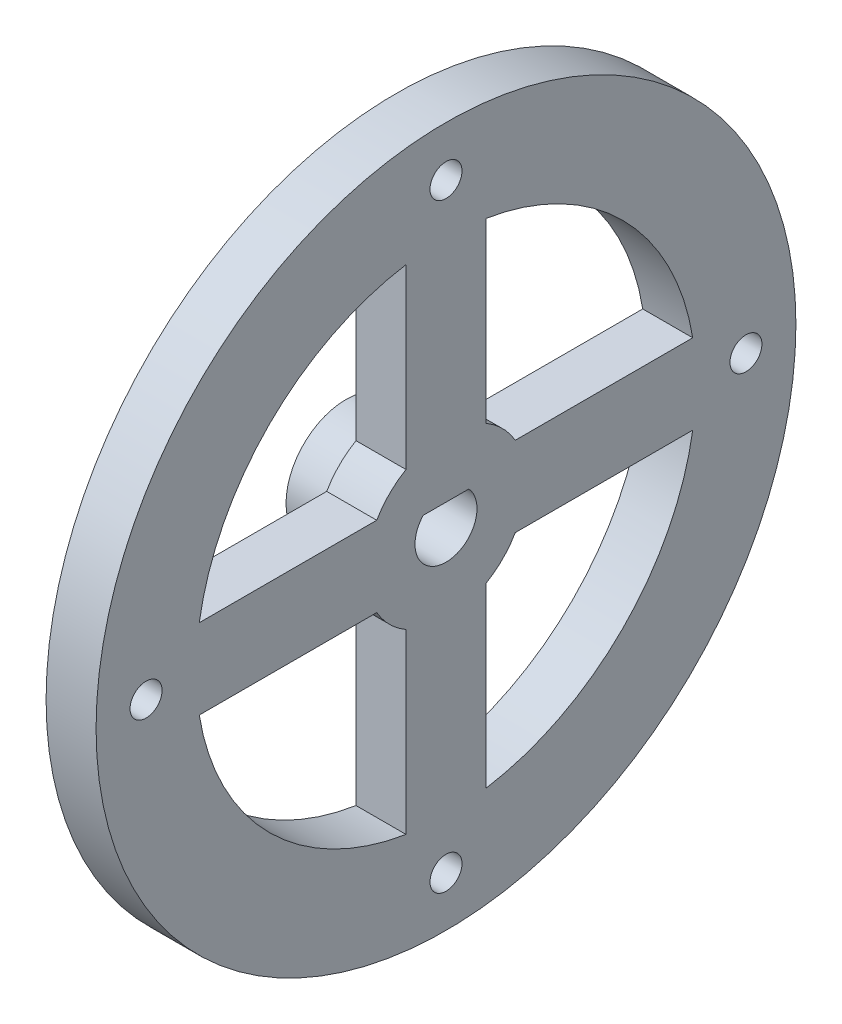
SolidWorks part; units mm, degrees
material "PLA (White)"
ref_plane "Front Plane" through (0, 0, 0) normal (0, 0, 1) x (1, 0, 0)
ref_plane "Top Plane" through (0, 0, 0) normal (0, 1, 0) x (1, 0, 0)
ref_plane "Right Plane" through (0, 0, 0) normal (1, 0, 0) x (0, 0, -1)
sketch "Sketch1" plane through (0, 0, 0) normal (1, 0, 0) x (0, 0, -1)
  line L0 (0, 0) -> (0, 50000) construction
  line L1 (4, 6.9282) -> (4, 24.6779)
  line L2 (-4, 24.6779) -> (-4, 6.9282)
  line L3 (-24.6779, -4) -> (-6.9282, -4)
  line L4 (-6.9282, 4) -> (-24.6779, 4)
  line L5 (4, -24.6779) -> (4, -6.9282)
  line L6 (-4, -6.9282) -> (-4, -24.6779)
  line L7 (24.6779, 4) -> (6.9282, 4)
  line L8 (6.9282, -4) -> (24.6779, -4)
  line L9 (2.2804, 2.1) -> (-2.2804, 2.1)
  circle A0 centre (0, 0) radius 35
  arc A1 (-2.2804, 2.1) -> (2.2804, 2.1) centre (0, 0) ccw
  arc A2 (-6.9282, -4) -> (-4, -6.9282) centre (0, 0) ccw
  arc A3 (-24.6779, -4) -> (-4, -24.6779) centre (0, 0) ccw
  arc A4 (-4, 6.9282) -> (-6.9282, 4) centre (0, 0) ccw
  arc A5 (24.6779, 4) -> (4, 24.6779) centre (0, 0) ccw
  arc A6 (4, -24.6779) -> (24.6779, -4) centre (0, 0) ccw
  arc A7 (4, -6.9282) -> (6.9282, -4) centre (0, 0) ccw
  arc A8 (6.9282, 4) -> (4, 6.9282) centre (0, 0) ccw
  arc A9 (-24.6779, 4) -> (-4, 24.6779) centre (0, 0) cw
  point P27 (0, 0)
  dimension "D1" = 70
  dimension "D2" = 6.2
  dimension "D5" = 16
  dimension "D6" = 50
  dimension "D3" = 8
  dimension "D7" = 2.1
  dimension "D4" = 4
extrude "Boss-Extrude1" add sketch "Sketch1" along normal blind 5
sketch "Sketch2" plane through (0, 0, 0) normal (-1, 0, 0) x (0, 0, 1)
  circle A0 centre (0, 0) radius 30 construction
  circle A1 centre (0, 30) radius 1.6
  circle A2 centre (30, 0) radius 1.6
  circle A3 centre (0, -30) radius 1.6
  circle A4 centre (-30, 0) radius 1.6
  point P14 (0, 0)
  dimension "D1" = 60
  dimension "D2" = 3.2
  dimension "D3" = 4
extrude "Cut-Extrude1" cut sketch "Sketch2" against normal through all
sketch "Sketch3" plane through (0, 0, 0) normal (-1, 0, 0) x (0, 0, 1)
  line L0 (-2.2804, 2.1) -> (2.2804, 2.1) construction
  line L1 (-2.2804, 2.1) -> (2.2804, 2.1)
  circle A2 centre (0, 0) radius 6
  arc A3 (-2.2804, 2.1) -> (2.2804, 2.1) centre (0, 0) ccw construction
  arc A4 (-2.2804, 2.1) -> (2.2804, 2.1) centre (0, 0) ccw
  dimension "D1" = 12
extrude "Boss-Extrude2" add sketch "Sketch3" along normal blind 5
sketch "Sketch6" plane through (0, 0, 0) normal (-1, 0, 0) x (0, 0, 1)
  circle A0 centre (0, 30) radius 4
  circle A1 centre (30, 0) radius 4
  circle A2 centre (0, -30) radius 4
  circle A3 centre (-30, 0) radius 4
  point P12 (0, 0)
  dimension "D1" = 8
  dimension "D2" = 4
extrude "Cut-Extrude2" cut sketch "Sketch6" against normal blind 2
sketch "Sketch7" plane through (-5, 0, 0) normal (-1, 0, 0) x (0, 0, 1)
  line L0 (-3.9116, -3.3007) -> (-3.9116, 3.3007)
  line L1 (3.9116, 3.3007) -> (3.9116, -3.3007)
  arc A2 (-3.9116, -3.3007) -> (3.9116, -3.3007) centre (0, 0) ccw
  arc A3 (3.9116, 3.3007) -> (-3.9116, 3.3007) centre (0, 0) ccw
  dimension "D2" = 10.2362
  dimension "D1" = 7.8232
extrude "Cut-Extrude3" cut sketch "Sketch7" against normal blind 2.3876 contours A3 L0 A2 L1
